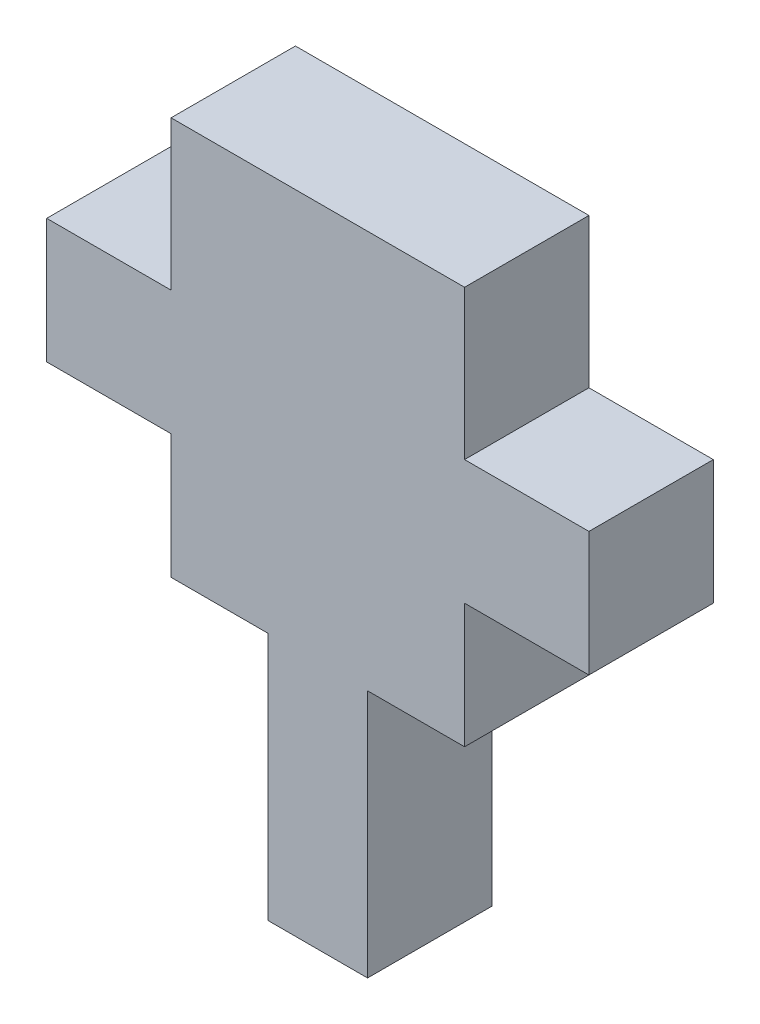
SolidWorks part; units mm, degrees
ref_plane "Plan de face" through (0, 0, 0) normal (0, 0, 1) x (1, 0, 0)
ref_plane "Plan de dessus" through (0, 0, 0) normal (0, 1, 0) x (1, 0, 0)
ref_plane "Plan de droite" through (0, 0, 0) normal (1, 0, 0) x (0, 0, -1)
sketch "Esquisse1" plane through (0, 0, 0) normal (0, 0, 1) x (1, 0, 0)
  line L1 (0, 0) -> (11.8, 0)
  line L2 (0, 0) -> (0, 16)
  line L3 (0, 16) -> (11.8, 16)
  line L4 (11.8, 0) -> (11.8, 16)
  line L5 (11.8, 5) -> (16.8, 5)
  line L6 (11.8, 5) -> (11.8, 10)
  line L7 (11.8, 10) -> (16.8, 10)
  line L8 (16.8, 5) -> (16.8, 10)
  line L9 (3.9, 0) -> (7.9, 0)
  line L10 (3.9, 0) -> (3.9, -10)
  line L11 (3.9, -10) -> (7.9, -10)
  line L12 (7.9, 0) -> (7.9, -10)
  line L13 (0, 10) -> (-5, 10)
  line L14 (0, 10) -> (0, 5)
  line L15 (0, 5) -> (-5, 5)
  line L16 (-5, 10) -> (-5, 5)
  dimension "D1" = 16
  dimension "D2" = 11.8
  dimension "D3" = 5
  dimension "D4" = 5
  dimension "D5" = 5
  dimension "D6" = 10
  dimension "D7" = 4
  dimension "D8" = 3.9
  dimension "D9" = 5
  dimension "D10" = 5
  dimension "D11" = 5
extrude "Boss.-Extru.1" add sketch "Esquisse1" along normal blind 5 contours L12 L1 L10 L11 | L13 L16 L15 L2 | L1 L4 L3 L2 | L5 L8 L7 L4
